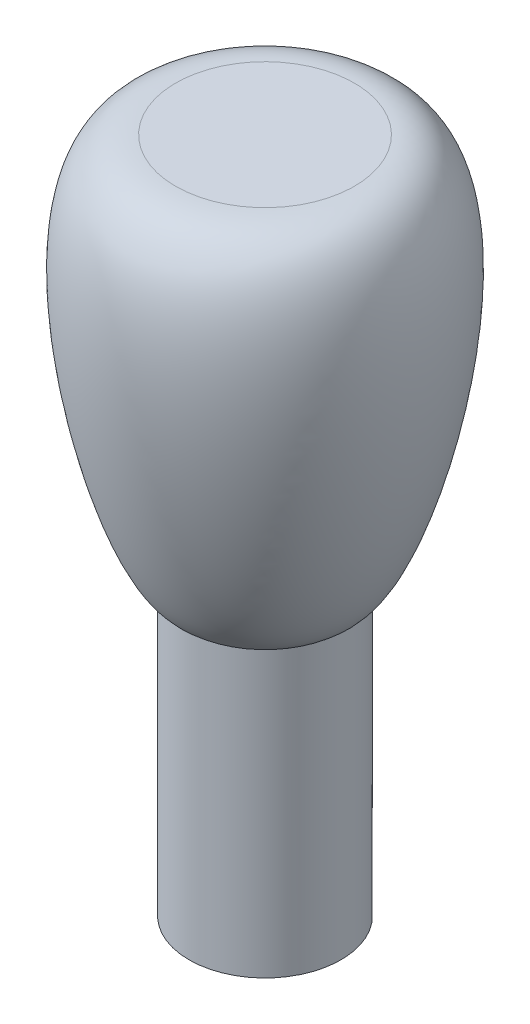
SolidWorks part; units mm, degrees
ref_plane "前视基准面" through (0, 0, 0) normal (0, 0, 1) x (1, 0, 0)
ref_plane "上视基准面" through (0, 0, 0) normal (0, 1, 0) x (1, 0, 0)
ref_plane "右视基准面" through (0, 0, 0) normal (1, 0, 0) x (0, 0, -1)
other "Configuration Table"
sketch "Sketch1" plane through (0, 0, 0) normal (0, 0, 1) x (1, 0, 0)
  line L0 (0, 21.3768) -> (0, 9)
  line L1 (0, 0) -> (2.4, 0)
  line L2 (0, 0) -> (0, 9)
  line L3 (0, 9) -> (2.4, 9)
  line L4 (2.4, 0) -> (2.4, 9)
  line L5 (0, 21.3768) -> (2.8248, 21.3768)
  line L6 (2.7861, 21.3768) -> (4.6886, 21.3768) construction
  spline S0 degree 3 poles (2.4, 9) (3.9436, 9.6401) (6.6782, 21.0057) (2.2387, 21.4613) (0.7533, 21.0089) (0, 21.3768) knots 0 0 0 0 0.7732 0.826737 1 1 1 1
  dimension "D1" = 2.4
  dimension "D2" = 9
revolve "Revolve1" add sketch "Sketch1" angle 360 about L0
sketch "Sketch2" plane through (0, 0, 0) normal (0, -1, 0) x (1, 0, 0)
  line L1 (-1.8735, -1.5) -> (1.8735, -1.5)
  circle A3 centre (0, 0) radius 2.4 construction
  arc A4 (-1.8735, -1.5) -> (1.8735, -1.5) centre (0, 0) ccw
  dimension "D1" = 1.5
extrude "Cut-Extrude1" cut sketch "Sketch2" against normal blind 3
